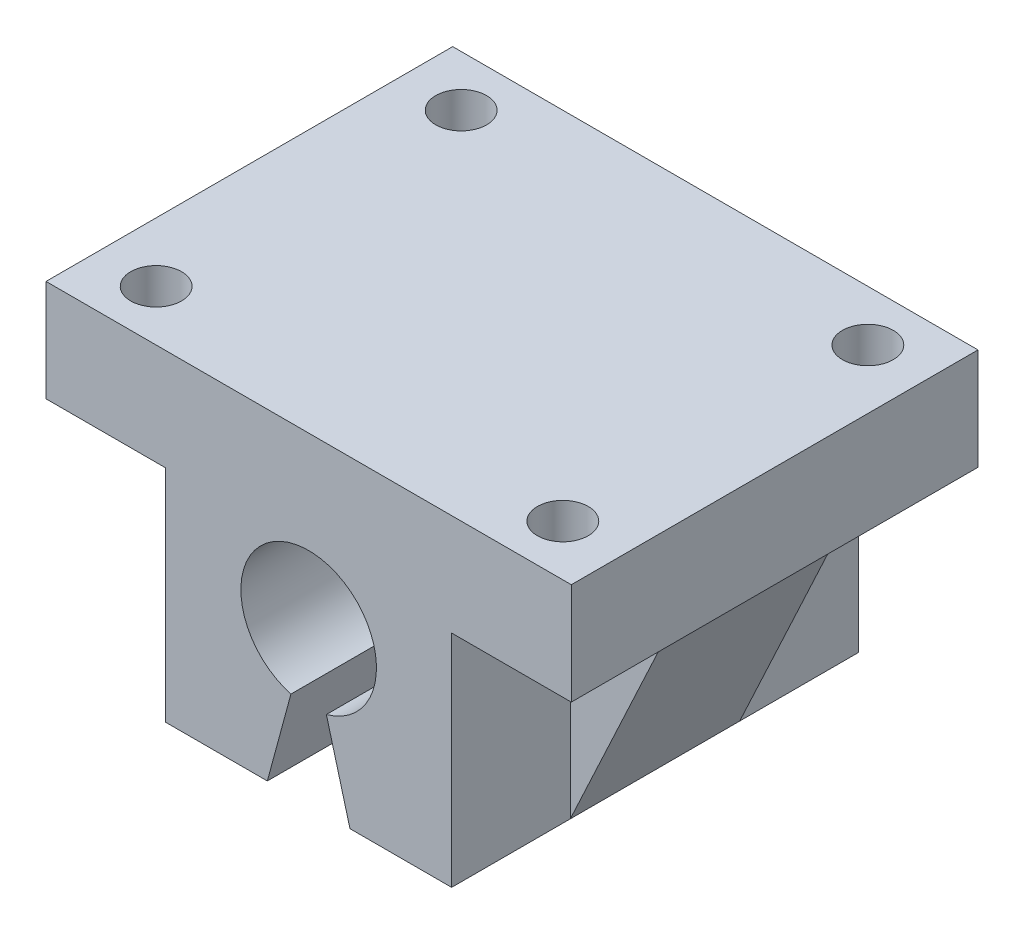
SolidWorks part; units mm, degrees
material "Aleación 1060"
ref_plane "Front Plane" through (0, 0, 0) normal (0, 0, 1) x (1, 0, 0)
ref_plane "Top Plane" through (0, 0, 0) normal (0, 1, 0) x (1, 0, 0)
ref_plane "Right Plane" through (0, 0, 0) normal (1, 0, 0) x (0, 0, -1)
sketch "Croquis1" plane through (0, 0, 0) normal (0, 0, 1) x (1, 0, 0)
  line L0 (15.5, 0) -> (-15.5, 0)
  line L1 (-15.5, 0) -> (-15.5, -6)
  line L2 (-15.5, -6) -> (-14.5, -6)
  line L3 (-14.5, -6) -> (-8.438, -19)
  line L4 (-8.438, -19) -> (-2.438, -19)
  line L5 (-2.438, -19) -> (0, -10)
  line L6 (0, -10) -> (2.438, -19)
  line L7 (2.438, -19) -> (8.438, -19)
  line L8 (8.438, -19) -> (14.5, -6)
  line L9 (14.5, -6) -> (15.5, -6)
  line L10 (15.5, -6) -> (15.5, 0)
  line L11 (-14.5, -6) -> (-8.438, -6)
  line L12 (-8.438, -6) -> (-8.438, -19)
  line L13 (8.438, -19) -> (8.438, -6)
  line L14 (8.438, -6) -> (14.5, -6)
  line L15 (-2.438, -19) -> (2.438, -19) construction
  line L16 (-8.438, -6) -> (8.438, -6) construction
  line L17 (0, -10) -> (0, 0) construction
  circle A0 centre (0, -10) radius 4
  point P4 (0, 0)
  dimension "D9" = 8
  dimension "D1" = 31
  dimension "D2" = 1
  dimension "D3" = 1
  dimension "D4" = 65
  dimension "D5" = 6
  dimension "D6" = 65
  dimension "D7" = 13
  dimension "D8" = 6
  dimension "D10" = 10
sketch "Croquis2" plane through (0, 0, 0) normal (0, 0, 1) x (1, 0, 0)
  line L0 (8.438, -6) -> (14.5, -6) construction
  line L2 (8.438, -19) -> (8.438, -6) construction
  line L3 (-8.438, -6) -> (-8.438, -19) construction
  line L4 (-14.5, -6) -> (-8.438, -6) construction
  line L6 (8.438, -6) -> (14.5, -6)
  line L8 (8.438, -19) -> (8.438, -6)
  line L9 (-8.438, -6) -> (-8.438, -19)
  line L10 (-14.5, -6) -> (-8.438, -6)
  line L12 (-8.438, -19) -> (-2.438, -19) construction
  line L13 (-8.438, -19) -> (-2.438, -19)
  line L14 (-15.5, 0) -> (-15.5, -6) construction
  line L15 (15.5, 0) -> (-15.5, 0) construction
  line L16 (15.5, -6) -> (15.5, 0) construction
  line L17 (0, -10) -> (2.438, -19) construction
  line L18 (-2.438, -19) -> (0, -10) construction
  line L19 (2.438, -19) -> (8.438, -19) construction
  line L20 (2.438, -19) -> (8.438, -19)
  line L21 (-2.438, -19) -> (0, -10)
  line L22 (0, -10) -> (2.438, -19)
  line L23 (15.5, -6) -> (15.5, 0)
  line L24 (15.5, 0) -> (-15.5, 0)
  line L25 (-15.5, 0) -> (-15.5, -6)
  line L26 (14.5, -6) -> (15.5, -6) construction
  line L27 (-15.5, -6) -> (-14.5, -6) construction
  line L28 (14.5, -6) -> (15.5, -6)
  line L29 (-15.5, -6) -> (-14.5, -6)
  circle A0 centre (0, -10) radius 4 construction
  circle A1 centre (0, -10) radius 4
extrude "Saliente-Extruir2" add sketch "Croquis2" along normal mid plane 24 contours A1 L22 L20 L8 L6 L28 L23 L24 L25 L29 L10 L9 L13 L21
sketch "Croquis3" plane through (0, 0, 0) normal (0, 0, 1) x (1, 0, 0)
  line L0 (8.438, -6) -> (14.5, -6) construction
  line L1 (8.438, -19) -> (14.5, -6) construction
  line L2 (8.438, -19) -> (8.438, -6) construction
  line L3 (-8.438, -6) -> (-8.438, -19) construction
  line L4 (-14.5, -6) -> (-8.438, -6) construction
  line L5 (-14.5, -6) -> (-8.438, -19) construction
  line L6 (8.438, -6) -> (14.5, -6)
  line L7 (8.438, -19) -> (14.5, -6)
  line L8 (8.438, -19) -> (8.438, -6)
  line L9 (-8.438, -6) -> (-8.438, -19)
  line L10 (-14.5, -6) -> (-8.438, -6)
  line L11 (-14.5, -6) -> (-8.438, -19)
extrude "Saliente-Extruir3" add sketch "Croquis3" along normal mid plane 10
sketch "Croquis4" plane through (0, 0, 0) normal (0, 1, 0) x (1, 0, 0)
  line L1 (12, -9) -> (-12, -9) construction
  line L2 (12, -9) -> (12, 9) construction
  line L3 (12, 9) -> (-12, 9) construction
  line L4 (-12, -9) -> (-12, 9) construction
  line L5 (12, -9) -> (-12, 9) construction
  line L6 (12, 9) -> (-12, -9) construction
  circle A0 centre (-12, 9) radius 1.5
  circle A1 centre (12, 9) radius 1.5
  circle A2 centre (12, -9) radius 1.5
  circle A3 centre (-12, -9) radius 1.5
  point P0 (0, 0)
  dimension "D1" = 3
  dimension "D2" = 24
  dimension "D3" = 18
extrude "Cortar-Extruir1" cut sketch "Croquis4" against normal up to next
